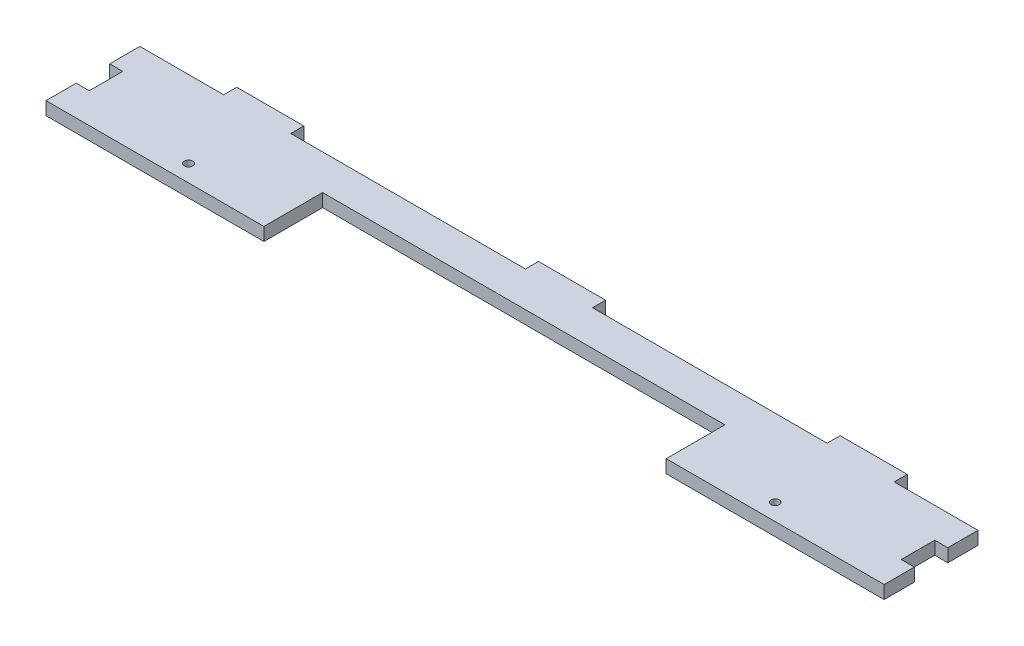
SolidWorks part; units mm, degrees
material "Very Low Density PE (SS)"
ref_plane "Front Plane" through (0, 0, 0) normal (0, 0, 1) x (1, 0, 0)
ref_plane "Top Plane" through (0, 0, 0) normal (0, 1, 0) x (1, 0, 0)
ref_plane "Right Plane" through (0, 0, 0) normal (1, 0, 0) x (0, 0, -1)
sketch "Sketch1" plane through (0, 0, 0) normal (0, 1, 0) x (1, 0, 0)
  line L0 (0, -14) -> (0, 15.95) construction
  line L1 (-125, 14) -> (-100, 14)
  line L2 (-125, 14) -> (-125, 5)
  line L3 (-125, -14) -> (125, -14)
  line L4 (125, 14) -> (125, 5)
  line L5 (-125, 14) -> (125, -14) construction
  line L6 (-125, -14) -> (125, 14) construction
  line L7 (100, 17.9) -> (80, 17.9)
  line L9 (-100, 14) -> (-100, 17.9)
  line L10 (-100, 17.9) -> (-80, 17.9)
  line L11 (-80, 14) -> (-80, 17.9)
  line L12 (80, 14) -> (80, 17.9)
  line L14 (100, 14) -> (100, 17.9)
  line L15 (-80, 14) -> (-10, 14)
  line L16 (100, 14) -> (125, 14)
  line L17 (10, 14) -> (80, 14)
  line L18 (-10, 17.9) -> (10, 17.9)
  line L19 (-10, 17.9) -> (-10, 14)
  line L21 (10, 17.9) -> (10, 14)
  line L22 (-10, 17.9) -> (10, 14) construction
  line L23 (-10, 14) -> (10, 17.9) construction
  line L24 (-125, -9) -> (125, -9) construction
  line L25 (121.1, 5) -> (125, 5)
  line L26 (-121.1, -5) -> (-125, -5)
  line L27 (-121.1, -5) -> (-121.1, 5)
  line L28 (-121.1, 5) -> (-125, 5)
  line L29 (-125, -5) -> (-125, 5) construction
  line L30 (-121.1, -5) -> (-125, 5) construction
  line L31 (-121.1, 5) -> (-125, -5) construction
  line L32 (125, -5) -> (125, 5) construction
  line L33 (121.1, -5) -> (125, -5)
  line L34 (121.1, -5) -> (121.1, 5)
  line L35 (-125, 5) -> (-125, -5) construction
  line L36 (-125, -5) -> (-125, -14)
  line L37 (125, 5) -> (125, -5) construction
  line L38 (125, -5) -> (125, -14)
  line L39 (-60, -14) -> (-60, 3.5)
  line L40 (-60, 3.5) -> (60, 3.5)
  line L41 (60, -14) -> (60, 3.5)
  circle A0 centre (-30, -9) radius 1.25
  circle A1 centre (-87.5, -9) radius 1.25
  circle A2 centre (30, -9) radius 1.25
  circle A3 centre (87.5, -9) radius 1.25
  point P0 (0, 0)
  point P18 (0, 15.95)
  point P31 (-123.05, 0)
  point P46 (0, 3.5)
  dimension "D8" = 2.5
  dimension "D10" = 2.5
  dimension "D12" = 10
  dimension "D1" = 250
  dimension "D2" = 28
  dimension "D3" = 20
  dimension "D4" = 3.9
  dimension "D5" = 25
  dimension "D6" = 20
  dimension "D7" = 5
  dimension "D9" = 30
  dimension "D11" = 87.5
  dimension "D13" = 3.9
  dimension "D14" = 17.5
  dimension "D15" = 60
extrude "Boss-Extrude1" add sketch "Sketch1" along normal blind 3.9 contours L41 L3 L38 L33 L34 L25 L4 L16 L14 L7 L12 L17 L21 L18 L19 L15 L11 L10 L9 L1 L2 L28 L27 L26 L36 L39 L40 A1 A3
